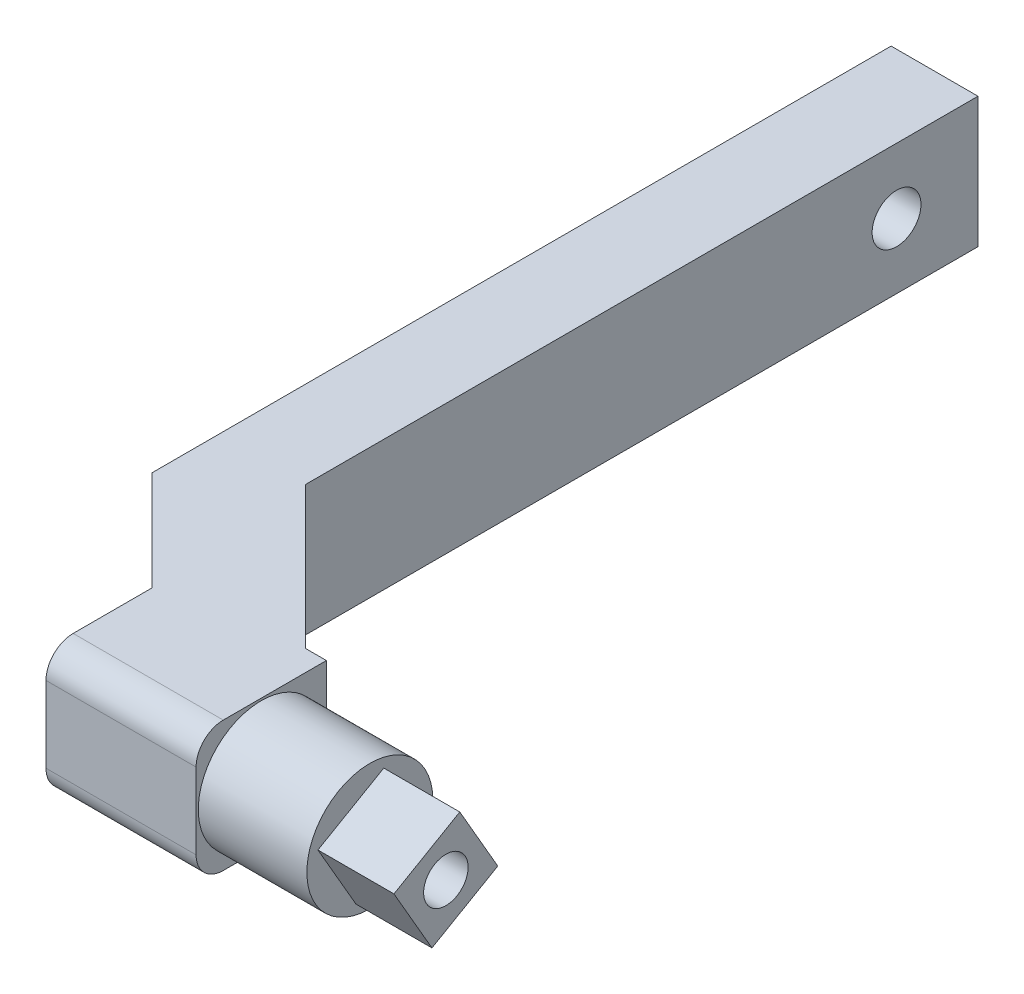
SolidWorks part; units mm, degrees
ref_plane "Front Plane" through (0, 0, 0) normal (0, 0, 1) x (1, 0, 0)
ref_plane "Top Plane" through (0, 0, 0) normal (0, 1, 0) x (1, 0, 0)
ref_plane "Right Plane" through (0, 0, 0) normal (1, 0, 0) x (0, 0, -1)
sketch "Эскиз1" plane through (0, 0, 0) normal (0, 1, 0) x (1, 0, 0)
  line L0 (0, 0) -> (-14.1421, -14.1421)
  line L1 (0, 0) -> (-37.8579, 37.8579)
  line L2 (-14.1421, -14.1421) -> (-52, 23.7157)
  line L3 (-37.8579, 37.8579) -> (-52, 23.7157)
  line L4 (-33.6421, 5.3579) -> (-33.6421, -14.1421)
  line L5 (-14.1421, -14.1421) -> (14, -14.1421)
  line L6 (-14.1421, -14.1421) -> (-14.1421, 9.8579)
  line L7 (-14.1421, 9.8579) -> (14, 9.8579)
  line L8 (14, -14.1421) -> (14, 9.8579)
  line L9 (-52, 23.7157) -> (-36, 23.7157)
  line L10 (-52, 23.7157) -> (-52, 159.8579)
  line L11 (-52, 159.8579) -> (-36, 159.8579)
  line L12 (-36, 23.7157) -> (-36, 159.8579)
  line L13 (-33.6421, -14.1421) -> (-14.1421, -14.1421)
  point P13 (14, -2.1421)
  dimension "D1" = 20
  dimension "D2" = 24
  dimension "D3" = 14
  dimension "D4" = 50
  dimension "D5" = 16
  dimension "D6" = 150
  dimension "D7" = 45
  dimension "D8" = 7.5
extrude "Бобышка-Вытянуть1" add sketch "Эскиз1" along normal blind 24 contours L1 L12 L11 L10 L3 | L9 L12 L1 L3 | L12 L9 L2 L6 L7 L1 | L7 L6 L0 L1 | L5 L8 L7 L1 L0 | L4 L13 L2
sketch "Эскиз2" plane through (14, 0, 0) normal (1, 0, 0) x (0, 0, -1)
  line L0 (-14.1421, 0) -> (9.8579, 24) construction
  circle A1 centre (-2.1421, 12) radius 11.6
  point P2 (0, 0)
  point P3 (-2.1421, 12)
  line M2 (-14.1421, 0) -> (9.8579, 0)
  line M3 (9.8579, 0) -> (9.8579, 24)
  line M4 (9.8579, 24) -> (-14.1421, 24)
  line M5 (-14.1421, 24) -> (-14.1421, 0)
  dimension "D1" = 23.2
extrude "Вырез-Вытянуть1" cut sketch "Эскиз2" against normal blind 20 contours A1 M5 M2 M3 M4 | L0 A1 M2 M3
sketch "Эскиз6" plane through (14, 0, 0) normal (1, 0, 0) x (0, 0, -1)
  circle A0 centre (-2.1421, 12) radius 4.1
extrude "Вырез-Вытянуть3" cut sketch "Эскиз6" against normal through all both and the other way through all
fillet "Скругление3" radius 5 2 edges at (-19.8211, 24, 14.1421) (-19.8211, 0, 14.1421)
sketch "Эскиз9" plane through (14, 0, 0) normal (1, 0, 0) x (0, 0, -1)
  line L0 (0.42, 21.5622) -> (-11.7043, 14.5622)
  line L1 (0.42, 21.5622) -> (7.42, 9.4378)
  line L2 (-11.7043, 14.5622) -> (-4.7043, 2.4378)
  line L3 (7.42, 9.4378) -> (-4.7043, 2.4378)
  line L4 (-2.1421, 23.6) -> (-2.1421, 0.4) construction
  line L5 (-2.1421, 12) -> (-7.9421, 22.0459) construction
  line L6 (7.42, 9.4378) -> (-11.7043, 14.5622) construction
  circle A1 centre (-2.1421, 12) radius 11.6 construction
  dimension "D1" = 14
  dimension "D2" = 14
  dimension "D3" = 30
extrude "Бобышка-Вытянуть2" add sketch "Эскиз9" along normal blind 14
sketch "Эскиз10" plane through (28, 0, 0) normal (1, 0, 0) x (0, 0, -1)
  circle A0 centre (-2.1421, 12) radius 4.1
  dimension "D1" = 8.2
extrude "Вырез-Вытянуть4" cut sketch "Эскиз10" against normal through all
sketch "Эскиз12" plane through (-52, 0, 0) normal (-1, 0, 0) x (0, 0, 1)
  line L0 (-159.8579, 24) -> (-159.8579, 0) construction
  line L1 (-144.8579, 0) -> (-144.8579, 24) construction
  line L2 (-23.7157, 0) -> (-159.8579, 0) construction
  line L3 (-23.7157, 24) -> (-159.8579, 24) construction
  circle A0 centre (-144.8579, 12) radius 11.1
  point P10 (0, 0)
  dimension "D1" = 15
extrude "Вырез-Вытянуть5" cut sketch "Эскиз12" against normal blind 7.1
sketch "Эскиз13" plane through (-44.9, 0, 0) normal (-1, 0, 0) x (0, 0, 1)
  circle A0 centre (-144.8579, 12) radius 4.5
extrude "Вырез-Вытянуть6" cut sketch "Эскиз13" against normal through all
